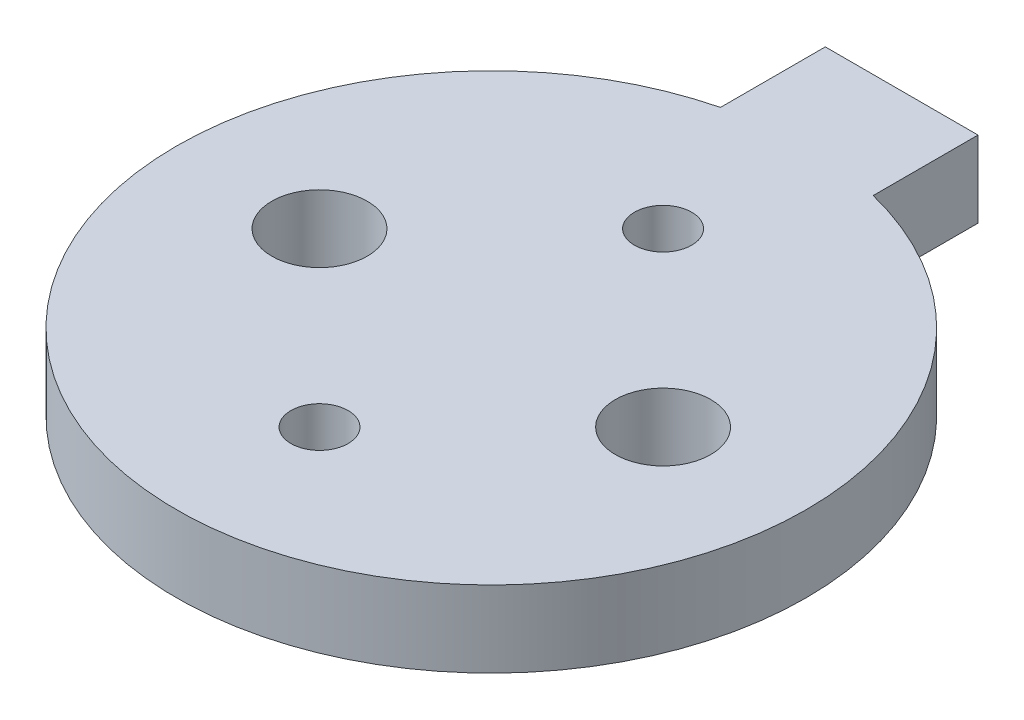
SolidWorks part; units mm, degrees
ref_plane "Front Plane" through (0, 0, 0) normal (0, 0, 1) x (1, 0, 0)
ref_plane "Top Plane" through (0, 0, 0) normal (0, 1, 0) x (1, 0, 0)
ref_plane "Right Plane" through (0, 0, 0) normal (1, 0, 0) x (0, 0, -1)
sketch "Sketch1" plane through (0, 0, 0) normal (0, 1, 0) x (1, 0, 0)
  circle A0 centre (0, 0) radius 33
  dimension "D1" = 66
extrude "Boss-Extrude1" add sketch "Sketch1" along normal blind 8
sketch "Sketch2" plane through (0, 8, 0) normal (0, 1, 0) x (1, 0, 0)
  line L0 (0, 0) -> (0, 47.1304) construction
  line L2 (-8, 43) -> (8, 43)
  line L3 (-8, 43) -> (-8, 32.0156)
  line L4 (-8, 32.0156) -> (8, 32.0156)
  line L5 (8, 43) -> (8, 32.0156)
  line L6 (-8, 43) -> (8, 32.0156) construction
  line L7 (-8, 32.0156) -> (8, 43) construction
  circle A0 centre (0, 0) radius 33 construction
  point P3 (0, 37.5078)
  dimension "D1" = 16
  dimension "D2" = 43
extrude "Boss-Extrude2" add sketch "Sketch2" against normal up to surface (8 mm away) up to face at (0, 0, 33)
sketch "Sketch3" plane through (0, 8, 0) normal (0, 1, 0) x (1, 0, 0)
  line L0 (-4.4, 0) -> (4.4, 0) construction
  line L1 (0, -4.4) -> (0, 4.4) construction
  circle A0 centre (0, 18) radius 3
  circle A1 centre (0, 0) radius 18 construction
  circle A2 centre (-18, 0) radius 5
  circle A3 centre (0, -18) radius 3
  circle A4 centre (18, 0) radius 5
  dimension "D1" = 36
  dimension "D2" = 6
  dimension "D3" = 10
extrude "Cut-Extrude1" cut sketch "Sketch3" against normal through all
